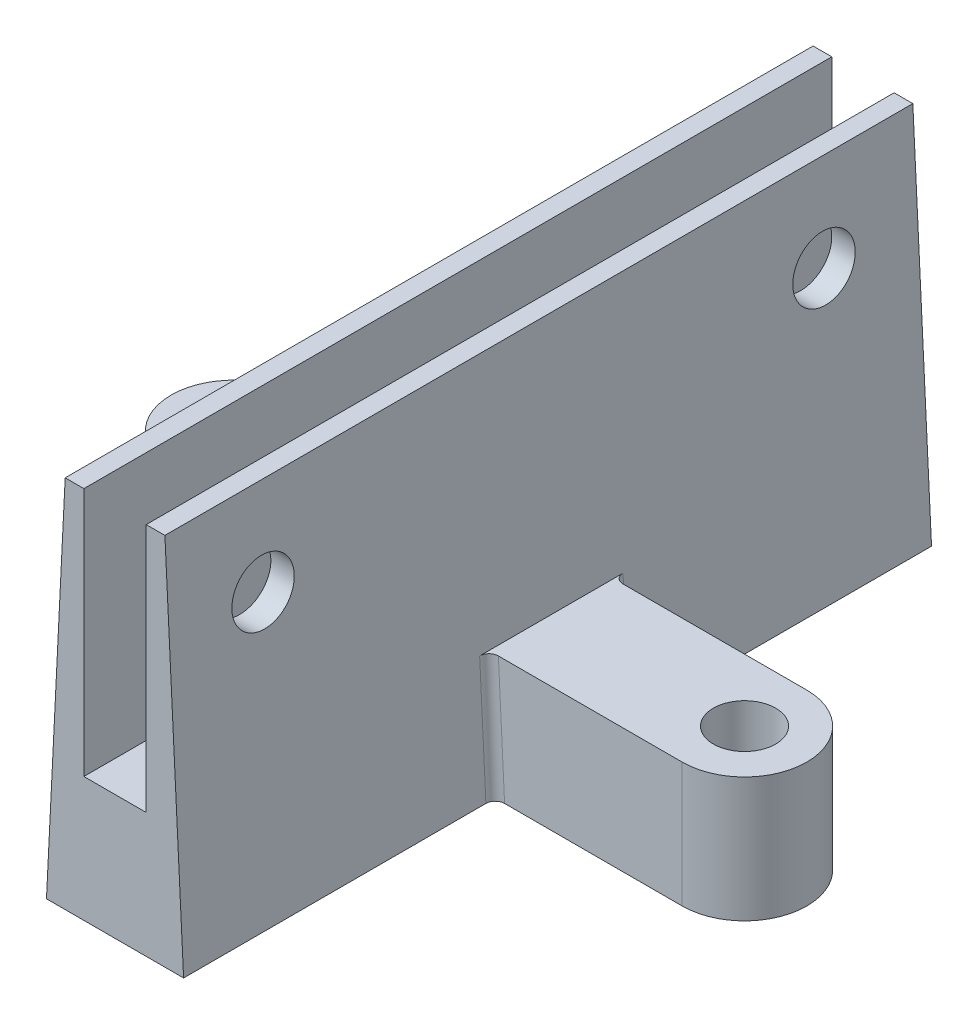
SolidWorks part; units mm, degrees
ref_plane "Front Plane" through (0, 0, 0) normal (0, 0, 1) x (1, 0, 0)
ref_plane "Top Plane" through (0, 0, 0) normal (0, 1, 0) x (1, 0, 0)
ref_plane "Right Plane" through (0, 0, 0) normal (1, 0, 0) x (0, 0, -1)
sketch "Sketch2" plane through (0, 0, 0) normal (0, 0, 1) x (1, 0, 0)
  line L40 (0, 0) -> (10, 0)
  line L41 (10, 0) -> (10, 40)
  line L42 (10, 40) -> (13, 40)
  line L46 (-3, 40) -> (0, 40)
  line L47 (0, 40) -> (0, 0)
  line L50 (16, -20) -> (13, 40)
  line L51 (-6, -20) -> (-3, 40)
  line L52 (-6, -20) -> (16, -20)
  dimension "D1" = 3
  dimension "D2" = 16
  dimension "D3" = 10
  dimension "D4" = 22
  dimension "D5" = 40
  dimension "D6" = 60
  dimension "D7" = 20
  dimension "D8" = 87.138
extrude "Boss-Extrude1" add sketch "Sketch2" against normal blind 120
sketch "Sketch5" plane through (0, -20, 0) normal (0, -1, 0) x (1, 0, 0)
  line L0 (16, -120) -> (16, 0) construction
  line L1 (16, -50) -> (46, -50)
  line L3 (16, -70) -> (46, -70)
  line L4 (46, -50) -> (46, -70) construction
  line L5 (-6, -120) -> (-6, 0) construction
  line L6 (-6, -50) -> (-36, -50)
  line L8 (-6, -70) -> (-36, -70)
  line L9 (-36, -50) -> (-36, -70) construction
  line L11 (16, -50) -> (13, -50)
  line L13 (16, -70) -> (13, -70)
  line L14 (13, -50) -> (13, -70)
  line L15 (-6, -70) -> (-3, -70)
  line L17 (-6, -50) -> (-3, -50)
  line L18 (-3, -70) -> (-3, -50)
  arc A0 (46, -70) -> (46, -50) centre (46, -60) ccw
  arc A1 (-36, -70) -> (-36, -50) centre (-36, -60) cw
  circle A2 centre (-36, -60) radius 5
  circle A3 centre (46, -60) radius 5
  dimension "D3" = 10
  dimension "D4" = 10
  dimension "D9" = 10
  dimension "D10" = 10
  dimension "D1" = 30
  dimension "D2" = 30
  dimension "D5" = 60
  dimension "D6" = 60
  dimension "D7" = 3
  dimension "D8" = 3
  dimension "D11" = 3
  dimension "D12" = 3
extrude "Boss-Extrude2" add sketch "Sketch5" against normal blind 20
fillet "Fillet1" radius 1.5 4 edges at (-5.5, -10, -50) (-5.5, -10, -70) (15.5, -10, -70) (15.5, -10, -50)
sketch "Sketch7" plane through (0, 0, 0) normal (1, 0, 0) x (0, 0, -1)
  line L0 (0, -20) -> (0, 40) construction
  line L1 (120, 40) -> (0, 40) construction
  line L2 (120, -20) -> (120, 40) construction
  circle A0 centre (15, 25) radius 5
  circle A1 centre (105, 25) radius 5
  dimension "D1" = 10
  dimension "D2" = 10
  dimension "D3" = 15
  dimension "D4" = 15
  dimension "D5" = 15
  dimension "D6" = 15
extrude "Cut-Extrude1" cut sketch "Sketch7" along normal through all both and the other way through all
